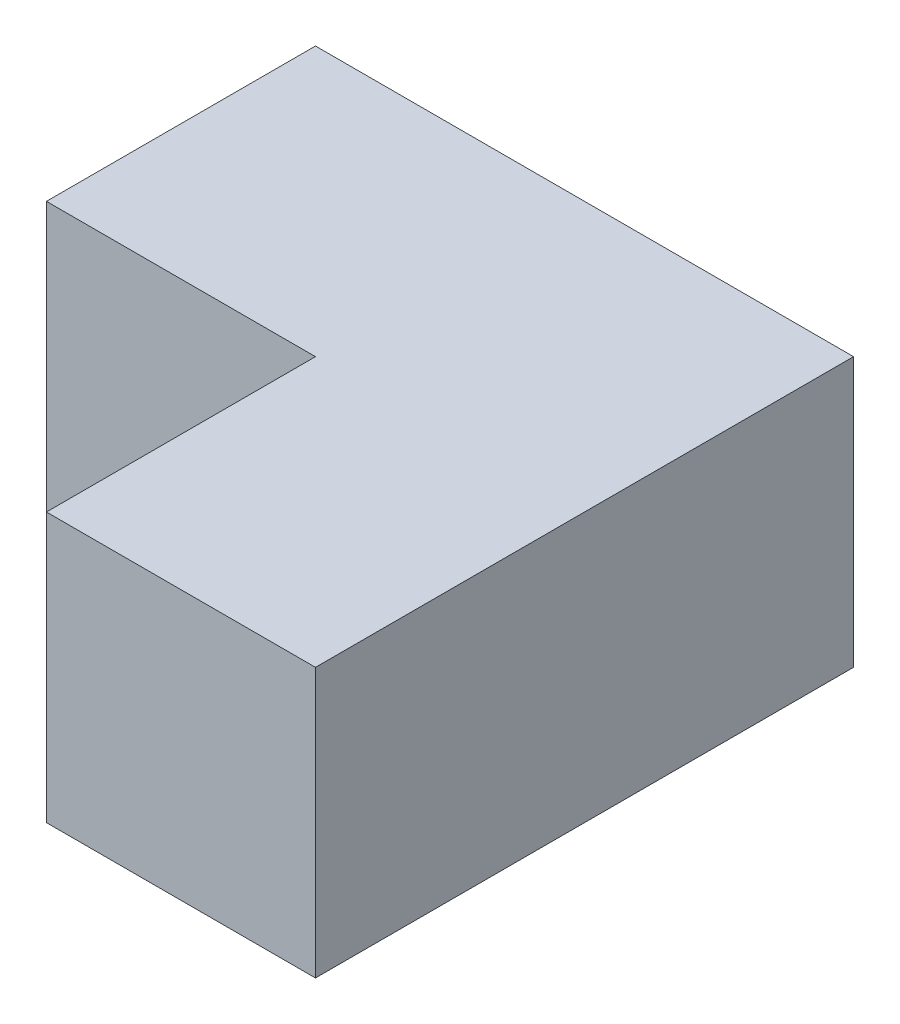
SolidWorks part; units mm, degrees
ref_plane "Alzado" through (0, 0, 0) normal (0, 0, 1) x (1, 0, 0)
ref_plane "Planta" through (0, 0, 0) normal (0, 1, 0) x (1, 0, 0)
ref_plane "Vista lateral" through (0, 0, 0) normal (1, 0, 0) x (0, 0, -1)
sketch "Croquis1" plane through (0, 0, 0) normal (0, 1, 0) x (1, 0, 0)
  line L0 (400, 200) -> (400, -200)
  line L1 (0, 0) -> (200, 0)
  line L2 (0, 0) -> (0, 200)
  line L3 (0, 200) -> (400, 200)
  line L6 (200, 0) -> (200, -200)
  line L7 (200, -200) -> (400, -200)
  dimension "D1" = 400
  dimension "D2" = 200
  dimension "D3" = 200
  dimension "D4" = 200
extrude "Saliente-Extruir1" add sketch "Croquis1" along normal blind 200
